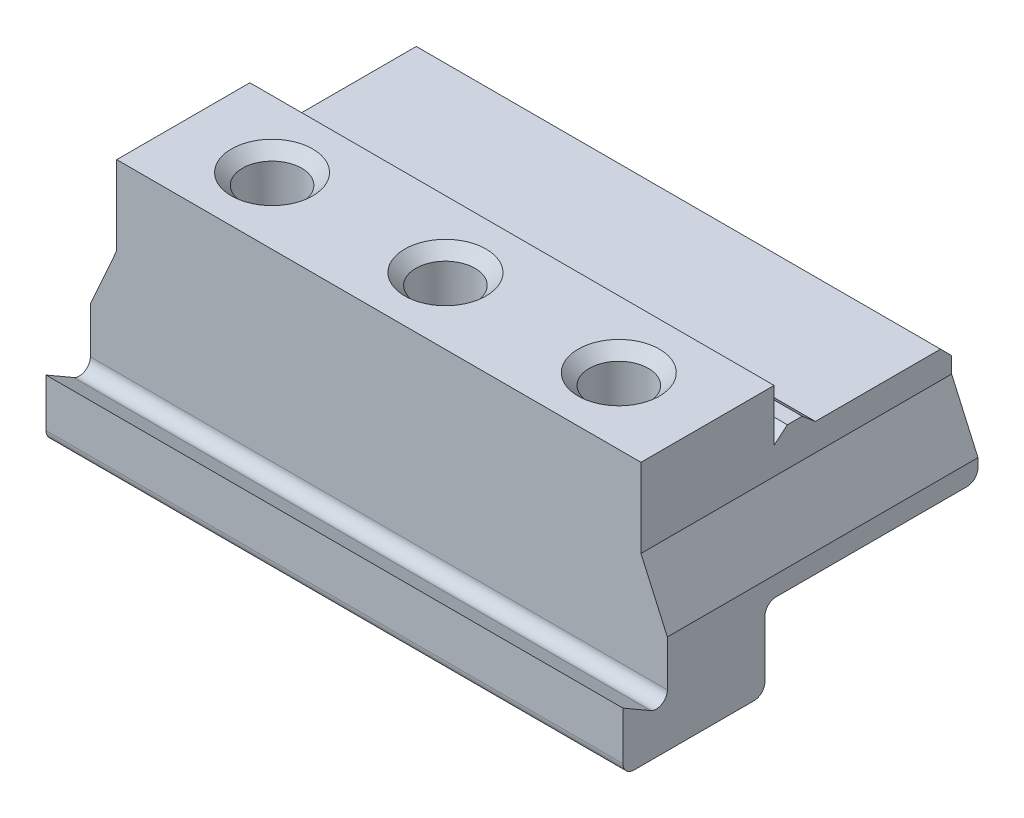
SolidWorks part; units mm, degrees
ref_plane "Front Plane" through (0, 0, 0) normal (0, 0, 1) x (1, 0, 0)
ref_plane "Top Plane" through (0, 0, 0) normal (0, 1, 0) x (1, 0, 0)
ref_plane "Right Plane" through (0, 0, 0) normal (1, 0, 0) x (0, 0, -1)
sketch "Sketch1" plane through (0, 0, 0) normal (1, 0, 0) x (0, 0, -1)
  line L0 (0, 1.5) -> (0, 8)
  line L1 (0, 8) -> (3.75, 5.8349)
  line L2 (6, 7.134) -> (6, 32)
  line L3 (6, 32) -> (24, 32)
  line L4 (1.5, 0) -> (17.7, 0)
  line L5 (19.2, 1.5) -> (19.2, 9.17)
  line L6 (20.7, 10.67) -> (46.5, 10.67)
  line L7 (24, 32) -> (24, 25)
  line L12 (48, 23.5) -> (48, 12.17)
  line L13 (24, 25) -> (25.7876, 26.5)
  line L14 (25.7876, 26.5) -> (27.7876, 26.5)
  line L15 (27.7876, 26.5) -> (29.5753, 25)
  line L16 (29.5753, 25) -> (46.5, 25)
  line L17 (46.5, 25) -> (48, 23.5)
  arc A0 (46.5, 10.67) -> (48, 12.17) centre (46.5, 12.17) ccw
  arc A1 (19.2, 9.17) -> (20.7, 10.67) centre (20.7, 9.17) cw
  arc A2 (17.7, 0) -> (19.2, 1.5) centre (17.7, 1.5) ccw
  arc A3 (0, 1.5) -> (1.5, 0) centre (1.5, 1.5) ccw
  arc A4 (3.75, 5.8349) -> (6, 7.134) centre (4.5, 7.134) ccw
  point P3 (48, 13.0141)
  point P14 (48, 25)
  point P23 (0, 0)
  point P28 (3.75, 10.67)
  dimension "D14" = 1.5
  dimension "D15" = 1.5
  dimension "D1" = 6
  dimension "D2" = 18
  dimension "D3" = 28.8
  dimension "D4" = 48
  dimension "D5" = 10.67
  dimension "D6" = 32
  dimension "D7" = 8
  dimension "D8" = 60
  dimension "D9" = 40
  dimension "D10" = 100
  dimension "D11" = 2
  dimension "D12" = 7
  dimension "D13" = 1.5
extrude "Boss-Extrude1" add sketch "Sketch1" along normal blind 78
sketch "Sketch2" plane through (0, 0, -6) normal (0, 0, 1) x (1, 0, 0)
  line L0 (78, 17.1919) -> (78, 32)
  line L1 (78, 32) -> (78, 7.134) construction
  line L2 (74.4382, 32) -> (74.4382, 21.33)
  line L3 (78, 32) -> (0, 32) construction
  line L4 (74.4382, 21.33) -> (78, 13.33)
  line L5 (74.4382, 32) -> (78, 32)
  line L6 (0, 17.1919) -> (0, 13.33)
  line L8 (0, 17.1919) -> (0, 32)
  line L9 (3.5618, 21.33) -> (0, 13.33)
  line L10 (3.5618, 32) -> (3.5618, 21.33)
  line L11 (3.5618, 32) -> (0, 32)
  line L12 (78, 17.1919) -> (78, 13.33)
  dimension "D1" = 24
  dimension "D2" = 10.67
  dimension "D3" = 8
extrude "Cut-Extrude1" cut sketch "Sketch2" against normal blind 78
sketch "Sketch3" plane through (0, 32, 0) normal (0, 1, 0) x (1, 0, 0)
  line L0 (74.4382, 48) -> (74.4382, 6) construction
  line L1 (3.5618, 24) -> (3.5618, 6) construction
  line L2 (74.4382, 24) -> (3.5618, 24) construction
  line L3 (74.4382, 24) -> (3.5618, 24) construction
  line L4 (15.5618, 15) -> (19.5618, 15) construction
  line L7 (58.4382, 15) -> (62.4382, 15) construction
  circle A0 centre (15.5618, 15) radius 4
  circle A1 centre (39, 15) radius 4
  circle A2 centre (62.4382, 15) radius 4
  dimension "D1" = 8
  dimension "D2" = 8
  dimension "D3" = 8
  dimension "D4" = 12
  dimension "D5" = 12
  dimension "D6" = 9
  dimension "D7" = 9
  dimension "D8" = 9
extrude "Cut-Extrude2" cut sketch "Sketch3" against normal blind 10
chamfer "Chamfer1" distance 1.5 angle 45 3 edges at (62.4382, 32, -11) (39, 32, -11) (15.5618, 32, -11)
